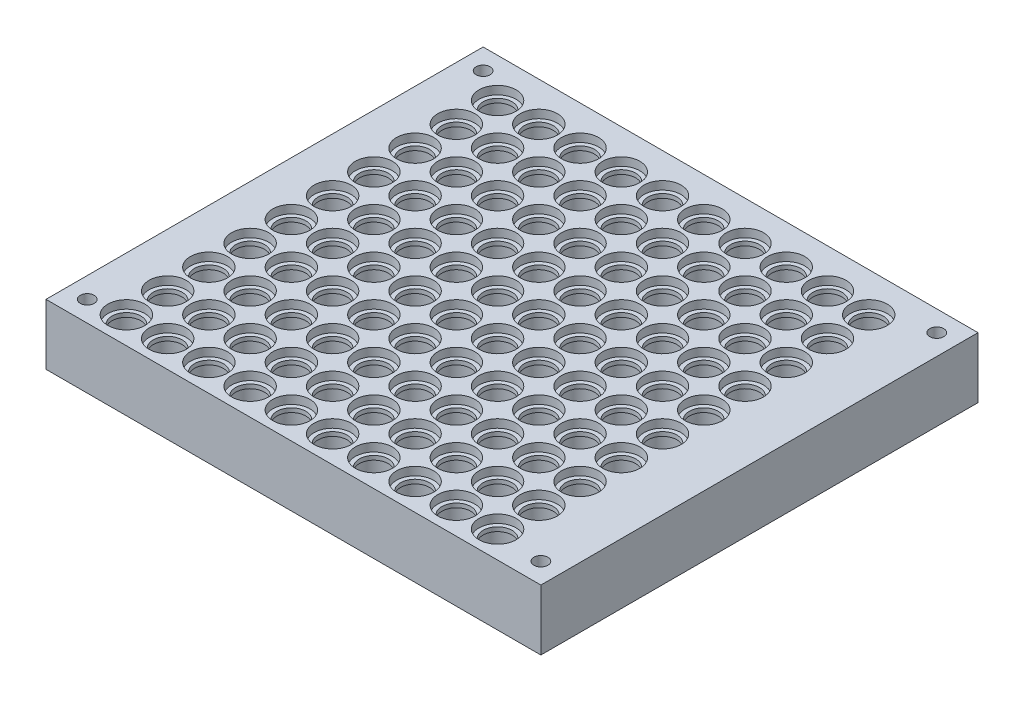
SolidWorks part; units mm, degrees
ref_plane "Front Plane" through (0, 0, 0) normal (0, 0, 1) x (1, 0, 0)
ref_plane "Top Plane" through (0, 0, 0) normal (0, 1, 0) x (1, 0, 0)
ref_plane "Right Plane" through (0, 0, 0) normal (1, 0, 0) x (0, 0, -1)
sketch "Sketch1" plane through (0, 0, 0) normal (0, 1, 0) x (1, 0, 0)
  line L0 (115, 101) -> (5, 101) construction
  line L1 (0, 0) -> (120, 0)
  line L2 (0, 0) -> (0, 106)
  line L3 (0, 106) -> (120, 106)
  line L4 (120, 0) -> (120, 106)
  line L6 (115, 101) -> (115, 5) construction
  circle A17 centre (13, 36.5) radius 4.5
  circle A18 centre (23, 36.5) radius 4.5
  circle A19 centre (13, 6.5) radius 4.5
  circle A28 centre (5, 5) radius 1.7
  circle A29 centre (5, 101) radius 1.7
  circle A30 centre (115, 101) radius 1.7
  circle A31 centre (115, 5) radius 1.7
  circle A32 centre (23, 6.5) radius 4.5
  circle A33 centre (33, 6.5) radius 4.5
  circle A34 centre (23, 16.5) radius 4.5
  circle A35 centre (33, 16.5) radius 4.5
  circle A36 centre (23, 26.5) radius 4.5
  circle A37 centre (33, 26.5) radius 4.5
  circle A38 centre (13, 16.5) radius 4.5
  circle A39 centre (13, 26.5) radius 4.5
  circle A40 centre (33, 36.5) radius 4.5
  circle A41 centre (13, 46.5) radius 4.5
  circle A42 centre (23, 46.5) radius 4.5
  circle A43 centre (33, 46.5) radius 4.5
  circle A44 centre (13, 56.5) radius 4.5
  circle A45 centre (23, 56.5) radius 4.5
  circle A46 centre (33, 56.5) radius 4.5
  circle A47 centre (13, 66.5) radius 4.5
  circle A48 centre (23, 66.5) radius 4.5
  circle A49 centre (33, 66.5) radius 4.5
  circle A50 centre (13, 76.5) radius 4.5
  circle A51 centre (23, 76.5) radius 4.5
  circle A52 centre (33, 76.5) radius 4.5
  circle A53 centre (13, 86.5) radius 4.5
  circle A54 centre (23, 86.5) radius 4.5
  circle A55 centre (33, 86.5) radius 4.5
  circle A56 centre (13, 96.5) radius 4.5
  circle A57 centre (23, 96.5) radius 4.5
  circle A58 centre (33, 96.5) radius 4.5
  circle A59 centre (43, 6.5) radius 4.5
  circle A60 centre (53, 6.5) radius 4.5
  circle A61 centre (63, 6.5) radius 4.5
  circle A62 centre (73, 6.5) radius 4.5
  circle A63 centre (83, 6.5) radius 4.5
  circle A64 centre (93, 6.5) radius 4.5
  circle A65 centre (103, 6.5) radius 4.5
  circle A66 centre (43, 16.5) radius 4.5
  circle A67 centre (53, 16.5) radius 4.5
  circle A68 centre (63, 16.5) radius 4.5
  circle A69 centre (73, 16.5) radius 4.5
  circle A70 centre (83, 16.5) radius 4.5
  circle A71 centre (93, 16.5) radius 4.5
  circle A72 centre (103, 16.5) radius 4.5
  circle A73 centre (43, 26.5) radius 4.5
  circle A74 centre (53, 26.5) radius 4.5
  circle A75 centre (63, 26.5) radius 4.5
  circle A76 centre (73, 26.5) radius 4.5
  circle A77 centre (83, 26.5) radius 4.5
  circle A78 centre (93, 26.5) radius 4.5
  circle A79 centre (103, 26.5) radius 4.5
  circle A80 centre (43, 36.5) radius 4.5
  circle A81 centre (53, 36.5) radius 4.5
  circle A82 centre (63, 36.5) radius 4.5
  circle A83 centre (73, 36.5) radius 4.5
  circle A84 centre (83, 36.5) radius 4.5
  circle A85 centre (93, 36.5) radius 4.5
  circle A86 centre (103, 36.5) radius 4.5
  circle A87 centre (43, 46.5) radius 4.5
  circle A88 centre (53, 46.5) radius 4.5
  circle A89 centre (63, 46.5) radius 4.5
  circle A90 centre (73, 46.5) radius 4.5
  circle A91 centre (83, 46.5) radius 4.5
  circle A92 centre (93, 46.5) radius 4.5
  circle A93 centre (103, 46.5) radius 4.5
  circle A94 centre (43, 56.5) radius 4.5
  circle A95 centre (53, 56.5) radius 4.5
  circle A96 centre (63, 56.5) radius 4.5
  circle A97 centre (73, 56.5) radius 4.5
  circle A98 centre (83, 56.5) radius 4.5
  circle A99 centre (93, 56.5) radius 4.5
  circle A100 centre (103, 56.5) radius 4.5
  circle A101 centre (43, 66.5) radius 4.5
  circle A102 centre (53, 66.5) radius 4.5
  circle A103 centre (63, 66.5) radius 4.5
  circle A104 centre (73, 66.5) radius 4.5
  circle A105 centre (83, 66.5) radius 4.5
  circle A106 centre (93, 66.5) radius 4.5
  circle A107 centre (103, 66.5) radius 4.5
  circle A108 centre (43, 76.5) radius 4.5
  circle A109 centre (53, 76.5) radius 4.5
  circle A110 centre (63, 76.5) radius 4.5
  circle A111 centre (73, 76.5) radius 4.5
  circle A112 centre (83, 76.5) radius 4.5
  circle A113 centre (93, 76.5) radius 4.5
  circle A114 centre (103, 76.5) radius 4.5
  circle A115 centre (43, 86.5) radius 4.5
  circle A116 centre (53, 86.5) radius 4.5
  circle A117 centre (63, 86.5) radius 4.5
  circle A118 centre (73, 86.5) radius 4.5
  circle A119 centre (83, 86.5) radius 4.5
  circle A120 centre (93, 86.5) radius 4.5
  circle A121 centre (103, 86.5) radius 4.5
  circle A122 centre (43, 96.5) radius 4.5
  circle A123 centre (53, 96.5) radius 4.5
  circle A124 centre (63, 96.5) radius 4.5
  circle A125 centre (73, 96.5) radius 4.5
  circle A126 centre (83, 96.5) radius 4.5
  circle A127 centre (93, 96.5) radius 4.5
  circle A128 centre (103, 96.5) radius 4.5
  point P7 (115, 53)
  point P9 (60, 101)
  point P10 (60, 106)
  point P20 (120, 53)
  dimension "D5" = 110
  dimension "D6" = 96
  dimension "D3" = 9
  dimension "D8" = 3.4
  dimension "D1" = 120
  dimension "D2" = 106
  dimension "D4" = 8
  dimension "D7" = 1.5
  dimension "D9" = 10
  dimension "D10" = 10
extrude "Boss-Extrude1" add sketch "Sketch1" along normal blind 14.7
sketch "Sketch2" plane through (0, 14.7, 0) normal (0, 1, 0) x (1, 0, 0)
  circle A0 centre (13, 6.5) radius 3.5
  circle A1 centre (13, 6.5) radius 4.5 construction
  circle A2 centre (13, 6.5) radius 5
  circle A3 centre (23, 6.5) radius 3.5
  circle A4 centre (23, 6.5) radius 5
  circle A5 centre (33, 6.5) radius 3.5
  circle A6 centre (33, 6.5) radius 5
  circle A7 centre (43, 6.5) radius 3.5
  circle A8 centre (43, 6.5) radius 5
  circle A9 centre (53, 6.5) radius 3.5
  circle A10 centre (53, 6.5) radius 5
  circle A11 centre (63, 6.5) radius 3.5
  circle A12 centre (63, 6.5) radius 5
  circle A13 centre (73, 6.5) radius 3.5
  circle A14 centre (73, 6.5) radius 5
  circle A15 centre (83, 6.5) radius 3.5
  circle A16 centre (83, 6.5) radius 5
  circle A17 centre (93, 6.5) radius 3.5
  circle A18 centre (93, 6.5) radius 5
  circle A19 centre (103, 6.5) radius 3.5
  circle A20 centre (103, 6.5) radius 5
  circle A21 centre (23, 16.5) radius 3.5
  circle A22 centre (23, 16.5) radius 5
  circle A23 centre (33, 16.5) radius 3.5
  circle A24 centre (33, 16.5) radius 5
  circle A25 centre (43, 16.5) radius 3.5
  circle A26 centre (43, 16.5) radius 5
  circle A27 centre (53, 16.5) radius 3.5
  circle A28 centre (53, 16.5) radius 5
  circle A29 centre (63, 16.5) radius 3.5
  circle A30 centre (63, 16.5) radius 5
  circle A31 centre (73, 16.5) radius 3.5
  circle A32 centre (73, 16.5) radius 5
  circle A33 centre (83, 16.5) radius 3.5
  circle A34 centre (83, 16.5) radius 5
  circle A35 centre (93, 16.5) radius 3.5
  circle A36 centre (93, 16.5) radius 5
  circle A37 centre (103, 16.5) radius 3.5
  circle A38 centre (103, 16.5) radius 5
  circle A39 centre (23, 26.5) radius 3.5
  circle A40 centre (23, 26.5) radius 5
  circle A41 centre (33, 26.5) radius 3.5
  circle A42 centre (33, 26.5) radius 5
  circle A43 centre (43, 26.5) radius 3.5
  circle A44 centre (43, 26.5) radius 5
  circle A45 centre (53, 26.5) radius 3.5
  circle A46 centre (53, 26.5) radius 5
  circle A47 centre (63, 26.5) radius 3.5
  circle A48 centre (63, 26.5) radius 5
  circle A49 centre (73, 26.5) radius 3.5
  circle A50 centre (73, 26.5) radius 5
  circle A51 centre (83, 26.5) radius 3.5
  circle A52 centre (83, 26.5) radius 5
  circle A53 centre (93, 26.5) radius 3.5
  circle A54 centre (93, 26.5) radius 5
  circle A55 centre (103, 26.5) radius 3.5
  circle A56 centre (103, 26.5) radius 5
  circle A57 centre (23, 36.5) radius 3.5
  circle A58 centre (23, 36.5) radius 5
  circle A59 centre (33, 36.5) radius 3.5
  circle A60 centre (33, 36.5) radius 5
  circle A61 centre (43, 36.5) radius 3.5
  circle A62 centre (43, 36.5) radius 5
  circle A63 centre (53, 36.5) radius 3.5
  circle A64 centre (53, 36.5) radius 5
  circle A65 centre (63, 36.5) radius 3.5
  circle A66 centre (63, 36.5) radius 5
  circle A67 centre (73, 36.5) radius 3.5
  circle A68 centre (73, 36.5) radius 5
  circle A69 centre (83, 36.5) radius 3.5
  circle A70 centre (83, 36.5) radius 5
  circle A71 centre (93, 36.5) radius 3.5
  circle A72 centre (93, 36.5) radius 5
  circle A73 centre (103, 36.5) radius 3.5
  circle A74 centre (103, 36.5) radius 5
  circle A75 centre (23, 46.5) radius 3.5
  circle A76 centre (23, 46.5) radius 5
  circle A77 centre (33, 46.5) radius 3.5
  circle A78 centre (33, 46.5) radius 5
  circle A79 centre (43, 46.5) radius 3.5
  circle A80 centre (43, 46.5) radius 5
  circle A81 centre (53, 46.5) radius 3.5
  circle A82 centre (53, 46.5) radius 5
  circle A83 centre (63, 46.5) radius 3.5
  circle A84 centre (63, 46.5) radius 5
  circle A85 centre (73, 46.5) radius 3.5
  circle A86 centre (73, 46.5) radius 5
  circle A87 centre (83, 46.5) radius 3.5
  circle A88 centre (83, 46.5) radius 5
  circle A89 centre (93, 46.5) radius 3.5
  circle A90 centre (93, 46.5) radius 5
  circle A91 centre (103, 46.5) radius 3.5
  circle A92 centre (103, 46.5) radius 5
  circle A93 centre (23, 56.5) radius 3.5
  circle A94 centre (23, 56.5) radius 5
  circle A95 centre (33, 56.5) radius 3.5
  circle A96 centre (33, 56.5) radius 5
  circle A97 centre (43, 56.5) radius 3.5
  circle A98 centre (43, 56.5) radius 5
  circle A99 centre (53, 56.5) radius 3.5
  circle A100 centre (53, 56.5) radius 5
  circle A101 centre (63, 56.5) radius 3.5
  circle A102 centre (63, 56.5) radius 5
  circle A103 centre (73, 56.5) radius 3.5
  circle A104 centre (73, 56.5) radius 5
  circle A105 centre (83, 56.5) radius 3.5
  circle A106 centre (83, 56.5) radius 5
  circle A107 centre (93, 56.5) radius 3.5
  circle A108 centre (93, 56.5) radius 5
  circle A109 centre (103, 56.5) radius 3.5
  circle A110 centre (103, 56.5) radius 5
  circle A111 centre (23, 66.5) radius 3.5
  circle A112 centre (23, 66.5) radius 5
  circle A113 centre (33, 66.5) radius 3.5
  circle A114 centre (33, 66.5) radius 5
  circle A115 centre (43, 66.5) radius 3.5
  circle A116 centre (43, 66.5) radius 5
  circle A117 centre (53, 66.5) radius 3.5
  circle A118 centre (53, 66.5) radius 5
  circle A119 centre (63, 66.5) radius 3.5
  circle A120 centre (63, 66.5) radius 5
  circle A121 centre (73, 66.5) radius 3.5
  circle A122 centre (73, 66.5) radius 5
  circle A123 centre (83, 66.5) radius 3.5
  circle A124 centre (83, 66.5) radius 5
  circle A125 centre (93, 66.5) radius 3.5
  circle A126 centre (93, 66.5) radius 5
  circle A127 centre (103, 66.5) radius 3.5
  circle A128 centre (103, 66.5) radius 5
  circle A129 centre (23, 76.5) radius 3.5
  circle A130 centre (23, 76.5) radius 5
  circle A131 centre (33, 76.5) radius 3.5
  circle A132 centre (33, 76.5) radius 5
  circle A133 centre (43, 76.5) radius 3.5
  circle A134 centre (43, 76.5) radius 5
  circle A135 centre (53, 76.5) radius 3.5
  circle A136 centre (53, 76.5) radius 5
  circle A137 centre (63, 76.5) radius 3.5
  circle A138 centre (63, 76.5) radius 5
  circle A139 centre (73, 76.5) radius 3.5
  circle A140 centre (73, 76.5) radius 5
  circle A141 centre (83, 76.5) radius 3.5
  circle A142 centre (83, 76.5) radius 5
  circle A143 centre (93, 76.5) radius 3.5
  circle A144 centre (93, 76.5) radius 5
  circle A145 centre (103, 76.5) radius 3.5
  circle A146 centre (103, 76.5) radius 5
  circle A147 centre (23, 86.5) radius 3.5
  circle A148 centre (23, 86.5) radius 5
  circle A149 centre (33, 86.5) radius 3.5
  circle A150 centre (33, 86.5) radius 5
  circle A151 centre (43, 86.5) radius 3.5
  circle A152 centre (43, 86.5) radius 5
  circle A153 centre (53, 86.5) radius 3.5
  circle A154 centre (53, 86.5) radius 5
  circle A155 centre (63, 86.5) radius 3.5
  circle A156 centre (63, 86.5) radius 5
  circle A157 centre (73, 86.5) radius 3.5
  circle A158 centre (73, 86.5) radius 5
  circle A159 centre (83, 86.5) radius 3.5
  circle A160 centre (83, 86.5) radius 5
  circle A161 centre (93, 86.5) radius 3.5
  circle A162 centre (93, 86.5) radius 5
  circle A163 centre (103, 86.5) radius 3.5
  circle A164 centre (103, 86.5) radius 5
  circle A165 centre (23, 96.5) radius 3.5
  circle A166 centre (23, 96.5) radius 5
  circle A167 centre (33, 96.5) radius 3.5
  circle A168 centre (33, 96.5) radius 5
  circle A169 centre (43, 96.5) radius 3.5
  circle A170 centre (43, 96.5) radius 5
  circle A171 centre (53, 96.5) radius 3.5
  circle A172 centre (53, 96.5) radius 5
  circle A173 centre (63, 96.5) radius 3.5
  circle A174 centre (63, 96.5) radius 5
  circle A175 centre (73, 96.5) radius 3.5
  circle A176 centre (73, 96.5) radius 5
  circle A177 centre (83, 96.5) radius 3.5
  circle A178 centre (83, 96.5) radius 5
  circle A179 centre (93, 96.5) radius 3.5
  circle A180 centre (93, 96.5) radius 5
  circle A181 centre (103, 96.5) radius 3.5
  circle A182 centre (103, 96.5) radius 5
  circle A183 centre (13, 16.5) radius 3.5
  circle A184 centre (13, 16.5) radius 5
  circle A185 centre (13, 26.5) radius 3.5
  circle A186 centre (13, 26.5) radius 5
  circle A187 centre (13, 36.5) radius 3.5
  circle A188 centre (13, 36.5) radius 5
  circle A189 centre (13, 46.5) radius 3.5
  circle A190 centre (13, 46.5) radius 5
  circle A191 centre (13, 56.5) radius 3.5
  circle A192 centre (13, 56.5) radius 5
  circle A193 centre (13, 66.5) radius 3.5
  circle A194 centre (13, 66.5) radius 5
  circle A195 centre (13, 76.5) radius 3.5
  circle A196 centre (13, 76.5) radius 5
  circle A197 centre (13, 86.5) radius 3.5
  circle A198 centre (13, 86.5) radius 5
  circle A199 centre (13, 96.5) radius 3.5
  circle A200 centre (13, 96.5) radius 5
  dimension "D1" = 7
  dimension "D2" = 10
  dimension "D3" = 10
extrude "Boss-Extrude2" add sketch "Sketch2" against normal blind 3
sketch "Sketch3" plane through (0, 14.7, 0) normal (0, 1, 0) x (1, 0, 0)
  circle A0 centre (13, 6.5) radius 4.5
  circle A1 centre (13, 6.5) radius 3.5 construction
  circle A2 centre (23, 6.5) radius 4.5
  circle A3 centre (33, 6.5) radius 4.5
  circle A4 centre (43, 6.5) radius 4.5
  circle A5 centre (53, 6.5) radius 4.5
  circle A6 centre (63, 6.5) radius 4.5
  circle A7 centre (73, 6.5) radius 4.5
  circle A8 centre (83, 6.5) radius 4.5
  circle A9 centre (93, 6.5) radius 4.5
  circle A10 centre (103, 6.5) radius 4.5
  circle A11 centre (23, 16.5) radius 4.5
  circle A12 centre (33, 16.5) radius 4.5
  circle A13 centre (43, 16.5) radius 4.5
  circle A14 centre (53, 16.5) radius 4.5
  circle A15 centre (63, 16.5) radius 4.5
  circle A16 centre (73, 16.5) radius 4.5
  circle A17 centre (83, 16.5) radius 4.5
  circle A18 centre (93, 16.5) radius 4.5
  circle A19 centre (103, 16.5) radius 4.5
  circle A20 centre (23, 26.5) radius 4.5
  circle A21 centre (33, 26.5) radius 4.5
  circle A22 centre (43, 26.5) radius 4.5
  circle A23 centre (53, 26.5) radius 4.5
  circle A24 centre (63, 26.5) radius 4.5
  circle A25 centre (73, 26.5) radius 4.5
  circle A26 centre (83, 26.5) radius 4.5
  circle A27 centre (93, 26.5) radius 4.5
  circle A28 centre (103, 26.5) radius 4.5
  circle A29 centre (23, 36.5) radius 4.5
  circle A30 centre (33, 36.5) radius 4.5
  circle A31 centre (43, 36.5) radius 4.5
  circle A32 centre (53, 36.5) radius 4.5
  circle A33 centre (63, 36.5) radius 4.5
  circle A34 centre (73, 36.5) radius 4.5
  circle A35 centre (83, 36.5) radius 4.5
  circle A36 centre (93, 36.5) radius 4.5
  circle A37 centre (103, 36.5) radius 4.5
  circle A38 centre (23, 46.5) radius 4.5
  circle A39 centre (33, 46.5) radius 4.5
  circle A40 centre (43, 46.5) radius 4.5
  circle A41 centre (53, 46.5) radius 4.5
  circle A42 centre (63, 46.5) radius 4.5
  circle A43 centre (73, 46.5) radius 4.5
  circle A44 centre (83, 46.5) radius 4.5
  circle A45 centre (93, 46.5) radius 4.5
  circle A46 centre (103, 46.5) radius 4.5
  circle A47 centre (23, 56.5) radius 4.5
  circle A48 centre (33, 56.5) radius 4.5
  circle A49 centre (43, 56.5) radius 4.5
  circle A50 centre (53, 56.5) radius 4.5
  circle A51 centre (63, 56.5) radius 4.5
  circle A52 centre (73, 56.5) radius 4.5
  circle A53 centre (83, 56.5) radius 4.5
  circle A54 centre (93, 56.5) radius 4.5
  circle A55 centre (103, 56.5) radius 4.5
  circle A56 centre (23, 66.5) radius 4.5
  circle A57 centre (33, 66.5) radius 4.5
  circle A58 centre (43, 66.5) radius 4.5
  circle A59 centre (53, 66.5) radius 4.5
  circle A60 centre (63, 66.5) radius 4.5
  circle A61 centre (73, 66.5) radius 4.5
  circle A62 centre (83, 66.5) radius 4.5
  circle A63 centre (93, 66.5) radius 4.5
  circle A64 centre (103, 66.5) radius 4.5
  circle A65 centre (23, 76.5) radius 4.5
  circle A66 centre (33, 76.5) radius 4.5
  circle A67 centre (43, 76.5) radius 4.5
  circle A68 centre (53, 76.5) radius 4.5
  circle A69 centre (63, 76.5) radius 4.5
  circle A70 centre (73, 76.5) radius 4.5
  circle A71 centre (83, 76.5) radius 4.5
  circle A72 centre (93, 76.5) radius 4.5
  circle A73 centre (103, 76.5) radius 4.5
  circle A74 centre (23, 86.5) radius 4.5
  circle A75 centre (33, 86.5) radius 4.5
  circle A76 centre (43, 86.5) radius 4.5
  circle A77 centre (53, 86.5) radius 4.5
  circle A78 centre (63, 86.5) radius 4.5
  circle A79 centre (73, 86.5) radius 4.5
  circle A80 centre (83, 86.5) radius 4.5
  circle A81 centre (93, 86.5) radius 4.5
  circle A82 centre (103, 86.5) radius 4.5
  circle A83 centre (23, 96.5) radius 4.5
  circle A84 centre (33, 96.5) radius 4.5
  circle A85 centre (43, 96.5) radius 4.5
  circle A86 centre (53, 96.5) radius 4.5
  circle A87 centre (63, 96.5) radius 4.5
  circle A88 centre (73, 96.5) radius 4.5
  circle A89 centre (83, 96.5) radius 4.5
  circle A90 centre (93, 96.5) radius 4.5
  circle A91 centre (103, 96.5) radius 4.5
  circle A92 centre (13, 16.5) radius 4.5
  circle A93 centre (13, 26.5) radius 4.5
  circle A94 centre (13, 36.5) radius 4.5
  circle A95 centre (13, 46.5) radius 4.5
  circle A96 centre (13, 56.5) radius 4.5
  circle A97 centre (13, 66.5) radius 4.5
  circle A98 centre (13, 76.5) radius 4.5
  circle A99 centre (13, 86.5) radius 4.5
  circle A100 centre (13, 96.5) radius 4.5
  dimension "D1" = 9
  dimension "D2" = 10
extrude "Cut-Extrude1" cut sketch "Sketch3" against normal blind 2
equation "\"o\"= 10mm"
equation "\"P\"= 10"
